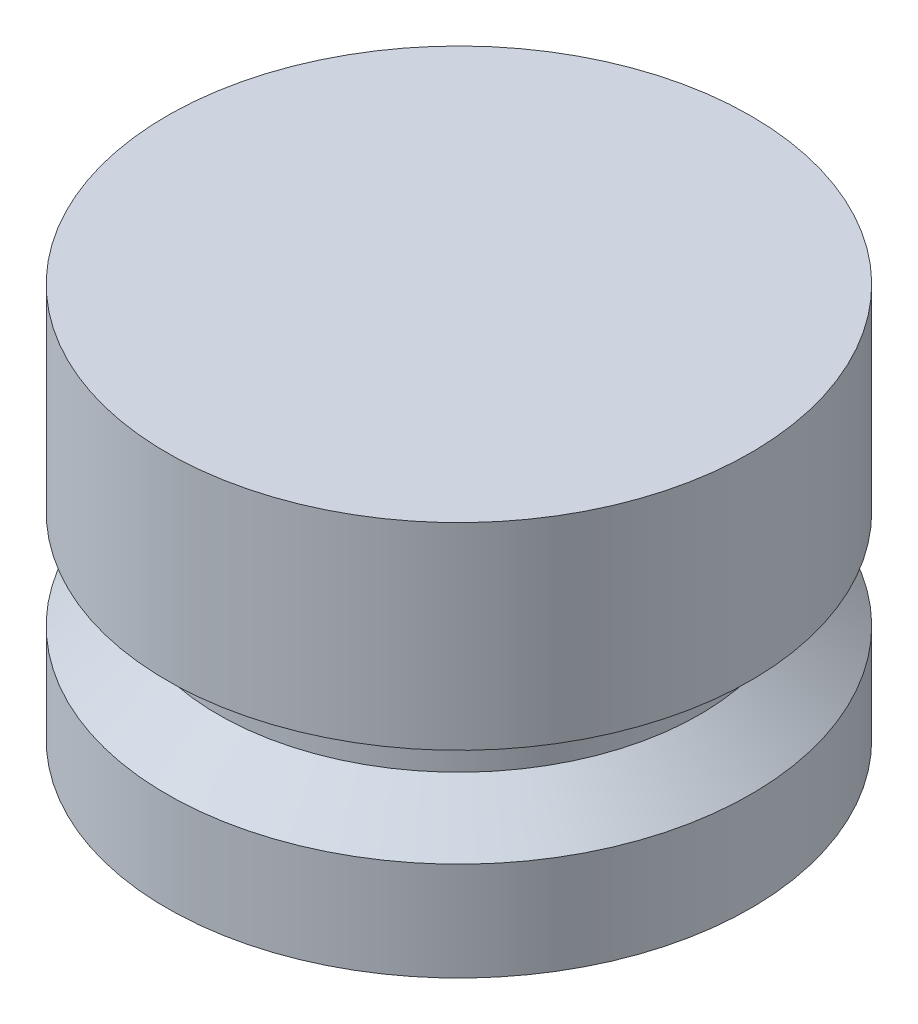
SolidWorks part; units mm, degrees
ref_plane "Front Plane" through (0, 0, 0) normal (0, 0, 1) x (1, 0, 0)
ref_plane "Top Plane" through (0, 0, 0) normal (0, 1, 0) x (1, 0, 0)
ref_plane "Right Plane" through (0, 0, 0) normal (1, 0, 0) x (0, 0, -1)
sketch "Sketch1" plane through (0, 0, 0) normal (0, 0, 1) x (1, 0, 0)
  line L0 (0, 0) -> (0, 12.7) construction
  line L1 (0, 0) -> (-9.398, 0)
  line L2 (-9.398, 0) -> (-9.398, 3.175)
  line L4 (-7.747, 4.572) -> (-7.747, 6.35)
  line L5 (-7.747, 6.35) -> (-9.398, 6.35)
  line L6 (-9.398, 6.35) -> (-9.398, 12.7)
  line L7 (-9.398, 12.7) -> (0, 12.7)
  line L8 (-9.525, 16.6801) -> (-9.525, -9.6051) construction
  line L9 (0, 0) -> (0, 12.7)
  line L10 (-7.747, 4.572) -> (-9.398, 3.175)
  dimension "D1" = 12.7
  dimension "D2" = 9.398
  dimension "D3" = 1.778
  dimension "D4" = 3.175
  dimension "D5" = 9.525
  dimension "D6" = 7.747
  dimension "D7" = 6.35
revolve "Revolve1" add sketch "Sketch1" angle 360 about L9
